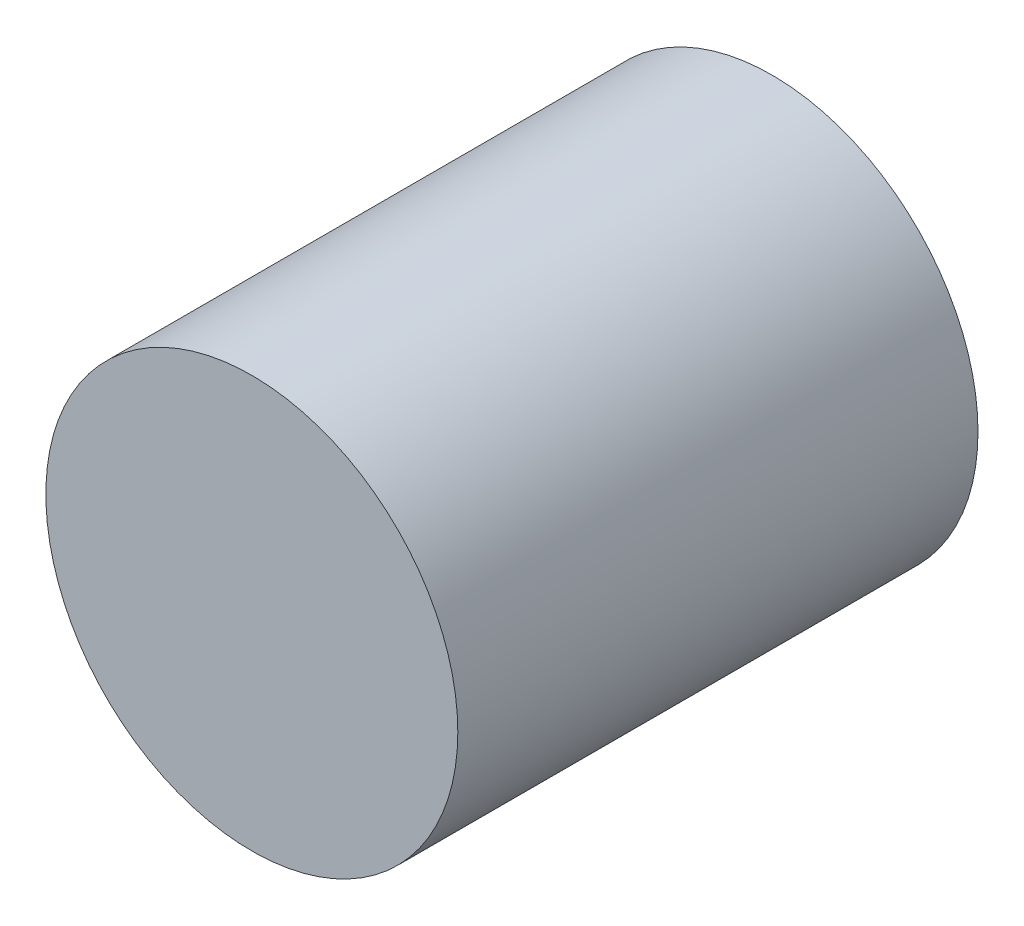
SolidWorks part; units mm, degrees
material "AISI 1020 Steel, Cold Rolled"
ref_plane "Front Plane" through (0, 0, 0) normal (0, 0, 1) x (1, 0, 0)
ref_plane "Top Plane" through (0, 0, 0) normal (0, 1, 0) x (1, 0, 0)
ref_plane "Right Plane" through (0, 0, 0) normal (1, 0, 0) x (0, 0, -1)
sketch "Sketch1" plane through (0, 0, 0) normal (0, 0, 1) x (1, 0, 0)
  circle A0 centre (0, 0) radius 7.92
  dimension "D1" = 15.84
extrude "Boss-Extrude1" add sketch "Sketch1" along normal blind 20
